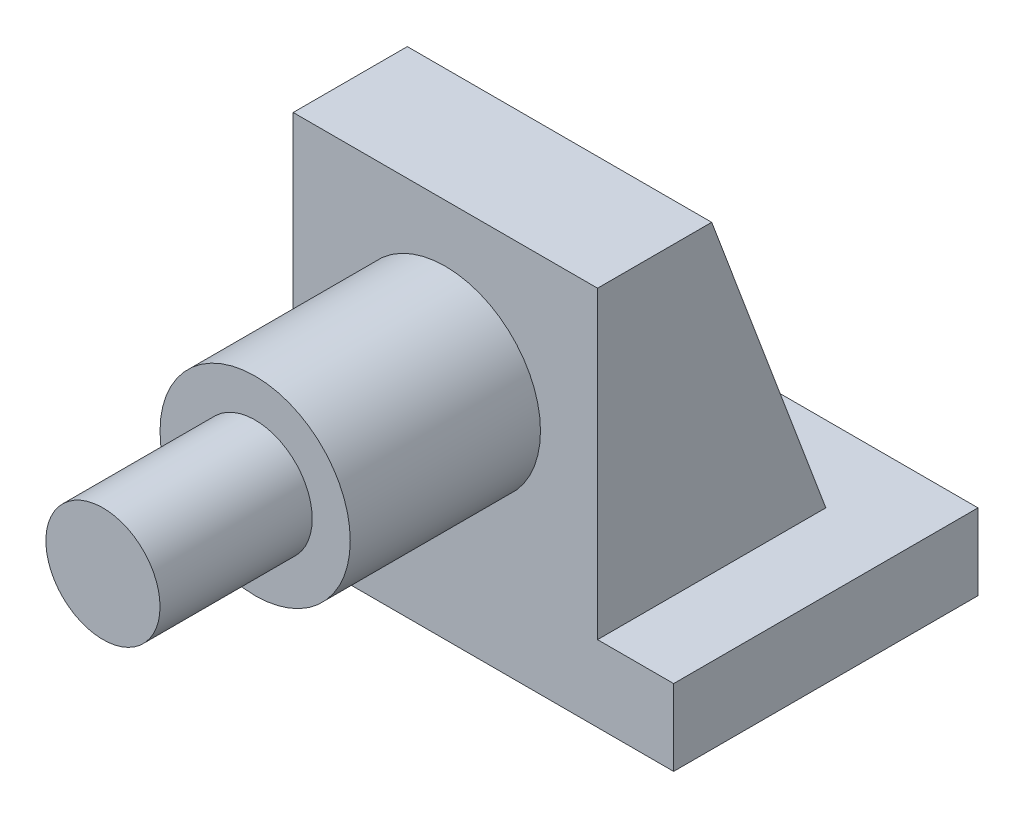
SolidWorks part; units mm, degrees
ref_plane "前视基准面" through (0, 0, 0) normal (0, 0, 1) x (1, 0, 0)
ref_plane "上视基准面" through (0, 0, 0) normal (0, 1, 0) x (1, 0, 0)
ref_plane "右视基准面" through (0, 0, 0) normal (1, 0, 0) x (0, 0, -1)
sketch "草图1" plane through (0, 0, 0) normal (0, 0, 1) x (1, 0, 0)
  line L0 (-20, -20) -> (-30, -20)
  line L1 (-20, 20) -> (20, 20)
  line L2 (-20, 20) -> (-20, -20)
  line L4 (20, 20) -> (20, -20)
  line L5 (-20, 20) -> (20, -20) construction
  line L6 (-20, -20) -> (20, 20) construction
  line L7 (30, -30) -> (-30, -30)
  line L8 (30, -30) -> (30, -20)
  line L9 (30, -20) -> (20, -20)
  line L10 (-30, -30) -> (-30, -20)
  line L11 (30, -30) -> (-30, -20) construction
  line L12 (30, -20) -> (-30, -30) construction
  point P0 (0, 0)
  point P6 (0, -25)
  dimension "D1" = 40
  dimension "D2" = 40
  dimension "D3" = 10
  dimension "D4" = 60
extrude "凸台-拉伸1" add sketch "草图1" along normal blind 40
sketch "草图2" plane through (20, 0, 0) normal (1, 0, 0) x (0, 0, -1)
  line L0 (0, -20) -> (-10, -20)
  line L2 (-40, -20) -> (0, -20) construction
  line L3 (-10, -20) -> (-25, 20)
  line L4 (-40, 20) -> (0, 20) construction
  line L5 (-25, 20) -> (0, 20)
  line L6 (0, 20) -> (0, -20)
  dimension "D1" = 10
  dimension "D2" = 25
extrude "切除-拉伸1" cut sketch "草图2" against normal blind 40
sketch "草图3" plane through (0, 0, 40) normal (0, 0, 1) x (1, 0, 0)
  circle A0 centre (0, 0) radius 12.5
  dimension "D1" = 25
extrude "凸台-拉伸2" add sketch "草图3" along normal blind 25
sketch "草图4" plane through (0, 0, 65) normal (0, 0, 1) x (1, 0, 0)
  circle A0 centre (0, 0) radius 7.5
  dimension "D1" = 15
extrude "凸台-拉伸3" add sketch "草图4" along normal blind 20
